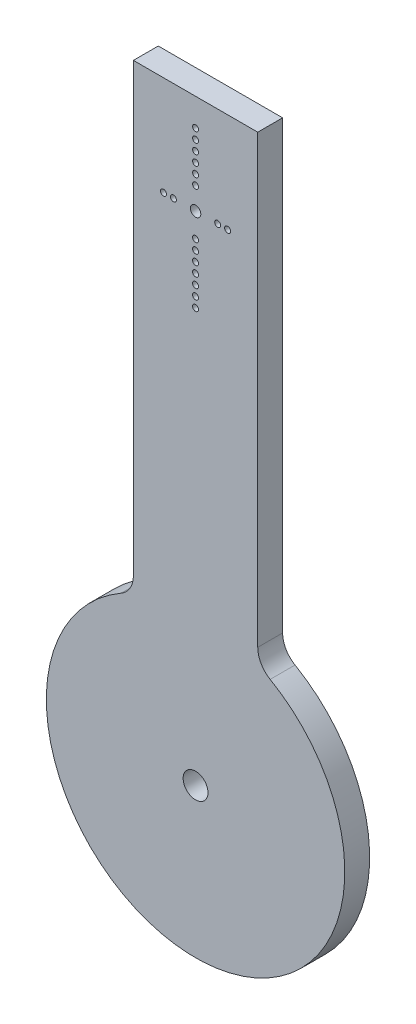
SolidWorks part; units mm, degrees
material "Maple"
ref_plane "Front Plane" through (0, 0, 0) normal (0, 0, 1) x (1, 0, 0)
ref_plane "Top Plane" through (0, 0, 0) normal (0, 1, 0) x (1, 0, 0)
ref_plane "Right Plane" through (0, 0, 0) normal (1, 0, 0) x (0, 0, -1)
sketch "Sketch1" plane through (0, 0, 0) normal (0, 0, 1) x (1, 0, 0)
  line L0 (0, 120) -> (0, 0) construction
  line L1 (-12.5, 120) -> (12.5, 120)
  line L2 (-12.5, 120) -> (-12.5, 30.3109)
  line L4 (12.5, 120) -> (12.5, 30.3109)
  arc A0 (-15, 25.9808) -> (15, 25.9808) centre (0, 0) ccw
  arc A1 (15, 25.9808) -> (12.5, 30.3109) centre (17.5, 30.3109) cw
  arc A2 (-15, 25.9808) -> (-12.5, 30.3109) centre (-17.5, 30.3109) ccw
  circle A3 centre (0, 100) radius 1.05 construction
  circle A4 centre (0, 95.15) radius 0.6 construction
  circle A5 centre (0, 93.15) radius 0.6 construction
  circle A6 centre (0, 91.15) radius 0.6 construction
  circle A7 centre (0, 89.15) radius 0.6 construction
  circle A8 centre (0, 87.15) radius 0.6 construction
  circle A9 centre (0, 85.15) radius 0.6 construction
  circle A10 centre (0, 83.15) radius 0.6 construction
  circle A11 centre (6.45, 100) radius 0.6 construction
  circle A12 centre (4.45, 100) radius 0.6 construction
  circle A13 centre (-4.45, 100) radius 0.6 construction
  circle A14 centre (-6.45, 100) radius 0.6 construction
  circle A15 centre (0, 104.45) radius 0.6 construction
  circle A16 centre (0, 106.45) radius 0.6 construction
  circle A17 centre (0, 108.45) radius 0.6 construction
  circle A18 centre (0, 110.45) radius 0.6 construction
  circle A19 centre (0, 112.45) radius 0.6 construction
  circle A20 centre (0, 114.45) radius 0.6 construction
  circle A21 centre (0, 100) radius 1.05
  circle A22 centre (0, 95.15) radius 0.6
  circle A23 centre (0, 93.15) radius 0.6
  circle A24 centre (0, 91.15) radius 0.6
  circle A25 centre (0, 89.15) radius 0.6
  circle A26 centre (0, 87.15) radius 0.6
  circle A27 centre (0, 85.15) radius 0.6
  circle A28 centre (0, 83.15) radius 0.6
  circle A29 centre (6.45, 100) radius 0.6
  circle A30 centre (4.45, 100) radius 0.6
  circle A31 centre (-4.45, 100) radius 0.6
  circle A32 centre (-6.45, 100) radius 0.6
  circle A33 centre (0, 104.45) radius 0.6
  circle A34 centre (0, 106.45) radius 0.6
  circle A35 centre (0, 108.45) radius 0.6
  circle A36 centre (0, 110.45) radius 0.6
  circle A37 centre (0, 112.45) radius 0.6
  circle A38 centre (0, 114.45) radius 0.6
  circle A39 centre (0, 0) radius 2.5
  dimension "D3" = 60
  dimension "D2" = 5
  dimension "D5" = 5
  dimension "D1" = 25
  dimension "D4" = 120
extrude "Boss-Extrude1" add sketch "Sketch1" along normal blind 5
